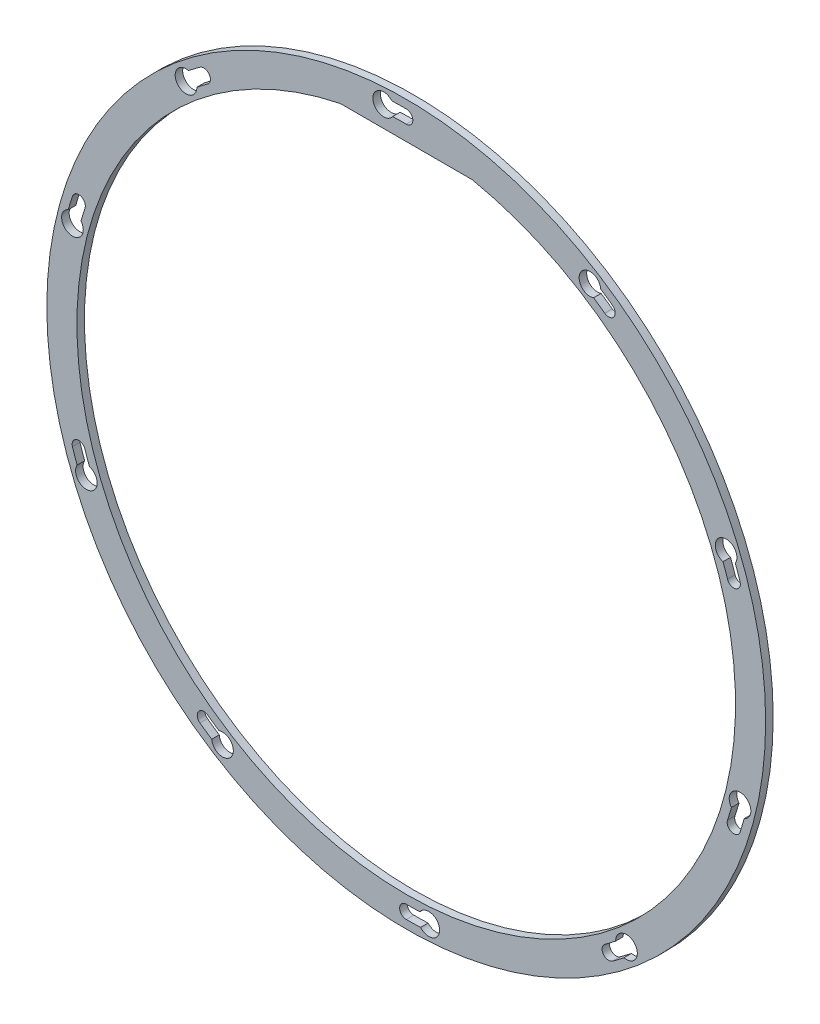
SolidWorks part; units mm, degrees
material "AISI 316 Stainless Steel Sheet (SS)"
ref_plane "Front Plane" through (0, 0, 0) normal (0, 0, 1) x (1, 0, 0)
ref_plane "Top Plane" through (0, 0, 0) normal (0, 1, 0) x (1, 0, 0)
ref_plane "Right Plane" through (0, 0, 0) normal (1, 0, 0) x (0, 0, -1)
sketch "Sketch1" plane through (0, 0, 0) normal (0, 0, 1) x (1, 0, 0)
  line L1 (-35, 171.4643) -> (35, 171.4643)
  arc A1 (-35, 171.4643) -> (35, 171.4643) centre (0, 0) ccw
  circle A2 centre (0, 0) radius 191
  dimension "D1" = 175
  dimension "D3" = 16
  dimension "D2" = 70
extrude "Boss-Extrude1" add sketch "Sketch1" along normal blind 4
hole_wizard "M6 Clearance Hole1" positions "Sketch2" profile "Sketch3" hole size "M6" standard "ISO" end condition through all
sketch "Sketch2" plane through (0, 0, 4) normal (0, 0, 1) x (1, 0, 0)
  circle A3 centre (0, 0) radius 183
  circle A4 centre (0, 0) radius 183
  point P10 (0, 183)
  dimension "D1" = 8
sketch "Sketch3" plane through (0, 183, 4) normal (1, 0, 0) x (0, -1, 0)
  line L0 (0, 0) -> (0, 4)
  line L1 (0, 4) -> (3.5, 4)
  line L2 (3.5, 4) -> (3.5, 0)
  line L5 (3.5, 0) -> (0, 0)
  line L11 (0, -6.35) -> (0, 107.95) construction
  dimension "Thru Hole Dia." = 7
  dimension "Thru Hole Depth" = 4
sketch "Sketch4" plane through (0, 0, 4) normal (0, 0, 1) x (1, 0, 0)
  line L0 (0, 186.5) -> (0, 179.5)
  circle A0 centre (0, 0) radius 183 construction
  arc A1 (-7.624, 186.3441) -> (-7.2523, 179.3534) centre (-11.9935, 182.6066) ccw
  circle A2 centre (0, 183) radius 3.5 construction
  arc A3 (0, 186.5) -> (-7.624, 186.3441) centre (0, 0) ccw
  arc A4 (0, 179.5) -> (-7.2523, 179.3534) centre (0, 0) ccw
  circle A5 centre (0, 183) radius 3.5 construction
  point P5 (0, 0)
  dimension "D1" = 11.5
  dimension "D2" = 12
extrude "Cut-Extrude3" cut sketch "Sketch4" against normal through all
pattern_circular "CirPattern1" count 10 over 360 about axis through (0, 0, 0) along (0, 0, 1) of "M6 Clearance Hole1", "Cut-Extrude3"
